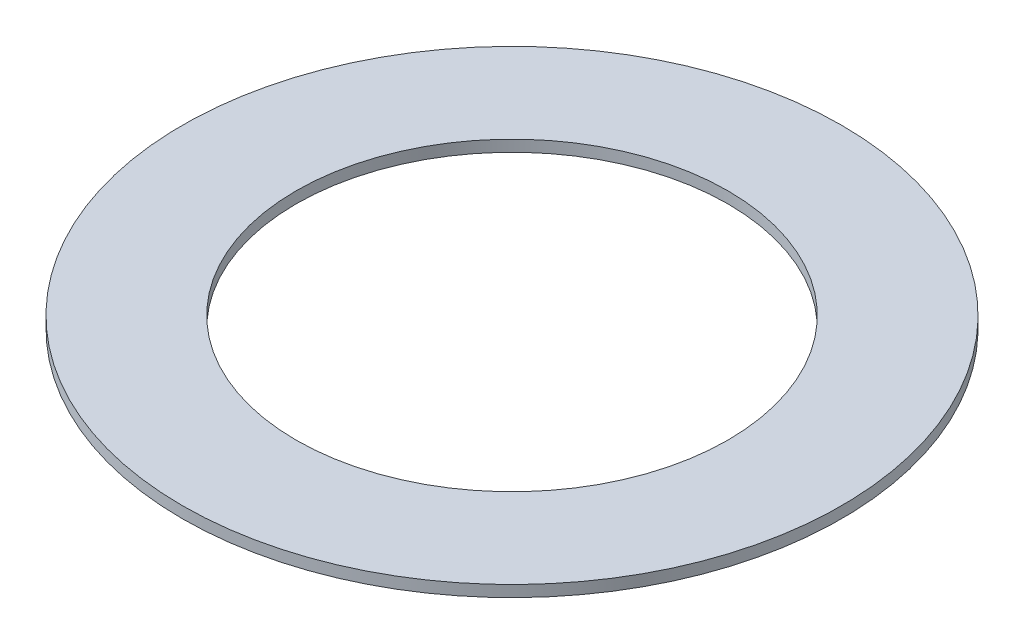
SolidWorks part; units mm, degrees
material "AISI 316 Chapa de acero inoxidable (SS)"
ref_plane "Alzado" through (0, 0, 0) normal (0, 0, 1) x (1, 0, 0)
ref_plane "Planta" through (0, 0, 0) normal (0, 1, 0) x (1, 0, 0)
ref_plane "Vista lateral" through (0, 0, 0) normal (1, 0, 0) x (0, 0, -1)
sketch "Croquis1" plane through (0, 0, 0) normal (0, 1, 0) x (1, 0, 0)
  circle A0 centre (0, 0) radius 14.5
  dimension "D1" = 29
extrude "Extruir-Lámina1" add sketch "Croquis1" along normal blind 0.5 thin thin type one direction reverse wall 5
